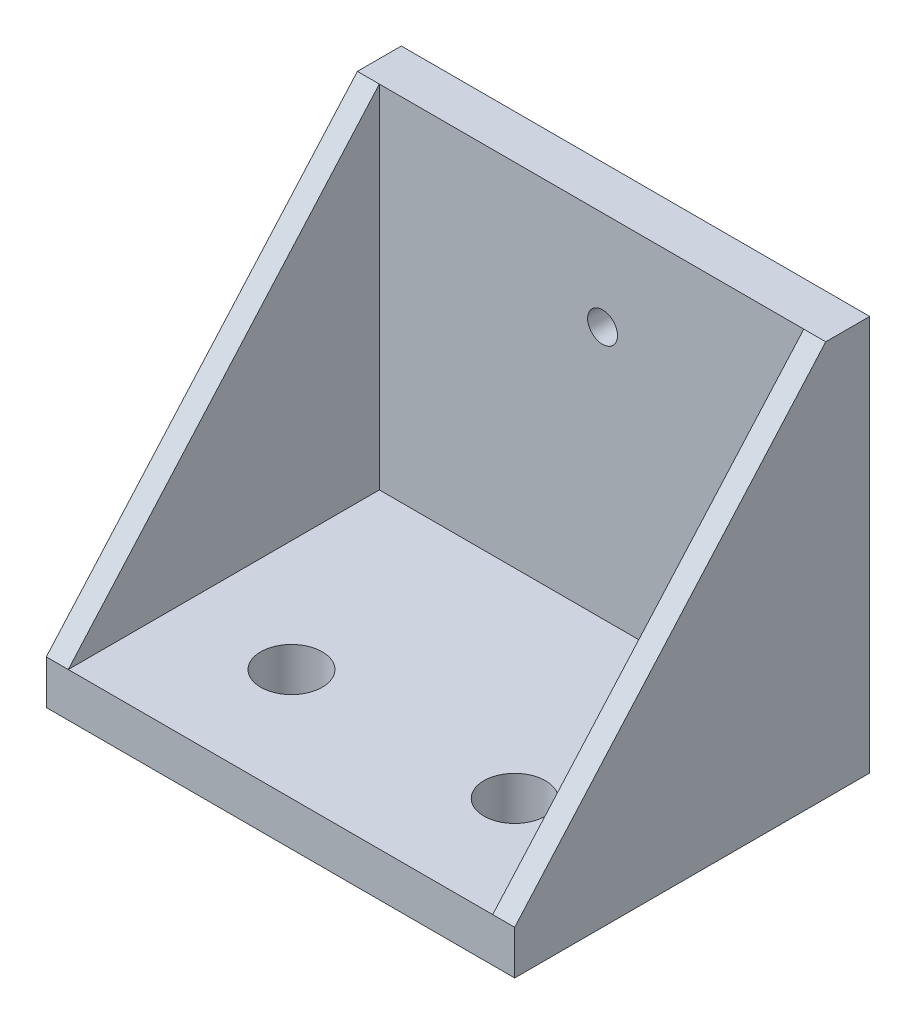
SolidWorks part; units mm, degrees
ref_plane "Front Plane" through (0, 0, 0) normal (0, 0, 1) x (1, 0, 0)
ref_plane "Top Plane" through (0, 0, 0) normal (0, 1, 0) x (1, 0, 0)
ref_plane "Right Plane" through (0, 0, 0) normal (1, 0, 0) x (0, 0, -1)
sketch "Sketch1" plane through (0, 0, 0) normal (0, 1, 0) x (1, 0, 0)
  line L0 (-12.7, 12.7) -> (-38.1, 12.7) construction
  line L1 (-50.8, 35.4) -> (0, 35.4)
  line L2 (-50.8, 35.4) -> (-50.8, 0)
  line L3 (-50.8, 0) -> (0, 0)
  line L4 (0, 35.4) -> (0, 0)
  circle A0 centre (-38.1, 12.7) radius 3.5
  circle A1 centre (-12.7, 12.7) radius 3.5
  point P9 (-25.4, 35.4)
  point P10 (-25.4, 12.7)
  dimension "D3" = 7
  dimension "D5" = 7
  dimension "D1" = 35.4
  dimension "D2" = 50.8
  dimension "D4" = 25.4
  dimension "D6" = 12.7
extrude "Boss-Extrude1" add sketch "Sketch1" along normal blind 5
sketch "Sketch2" plane through (0, 0, -35.4) normal (0, 0, -1) x (-1, 0, 0)
  line L1 (0, 0) -> (50.8, 0)
  line L2 (0, 0) -> (0, 45)
  line L3 (0, 45) -> (50.8, 45)
  line L4 (50.8, 0) -> (50.8, 45)
  dimension "D1" = 45
extrude "Boss-Extrude2" add sketch "Sketch2" along normal blind 5
sketch "Sketch3" plane through (0, 0, -40.4) normal (0, 0, -1) x (-1, 0, 0)
  line L0 (0, 0) -> (50.8, 0) construction
  line L1 (50.8, 45) -> (0, 45) construction
  circle A0 centre (25.4, 33.75) radius 1.7
  point P6 (25.4, 45)
  dimension "D2" = 3.4
  dimension "D1" = 33.75
extrude "Cut-Extrude1" cut sketch "Sketch3" against normal blind 5
sketch "Sketch4" plane through (0, 0, 0) normal (1, 0, 0) x (0, 0, -1)
  line L0 (0, 5) -> (35.4, 45)
  line L1 (35.4, 45) -> (40.4, 45)
  line L2 (40.4, 45) -> (40.4, 0)
  line L3 (40.4, 0) -> (0, 0)
  line L4 (0, 0) -> (0, 5)
extrude "Boss-Extrude3" add sketch "Sketch4" against normal blind 2.5
sketch "Sketch5" plane through (-50.8, 0, 0) normal (-1, 0, 0) x (0, 0, 1)
  line L0 (-35.4, 45) -> (-40.4, 45)
  line L1 (-40.4, 45) -> (-40.4, 0)
  line L2 (-40.4, 0) -> (0, 0)
  line L3 (0, 0) -> (0, 5)
  line L4 (0, 5) -> (-35.4, 45)
extrude "Boss-Extrude4" add sketch "Sketch5" along normal blind 2.5
